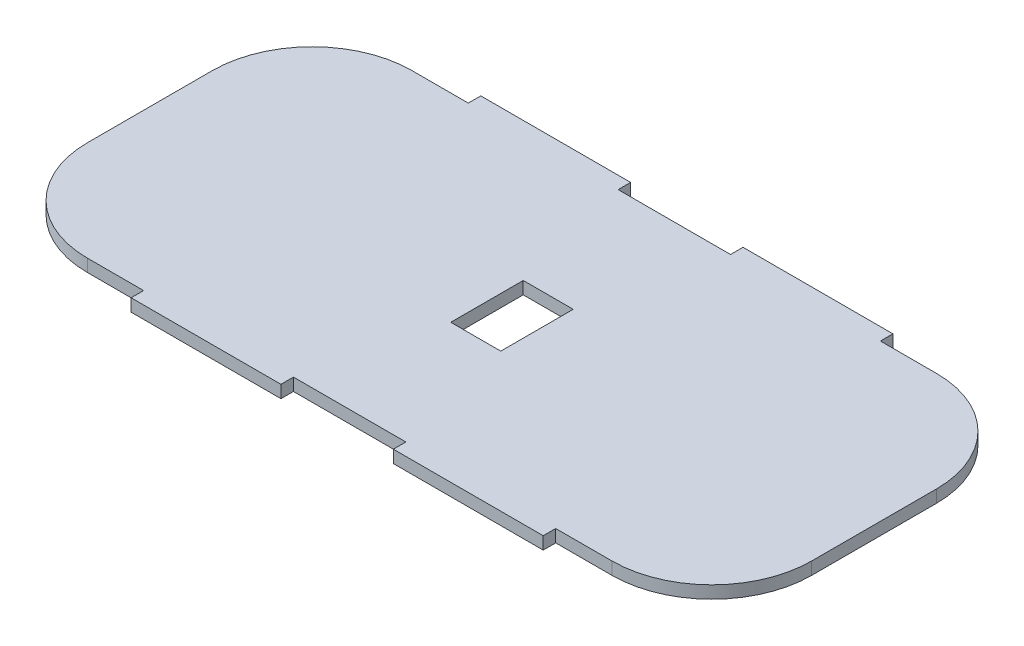
SolidWorks part; units mm, degrees
ref_plane "Front Plane" through (0, 0, 0) normal (0, 0, 1) x (1, 0, 0)
ref_plane "Top Plane" through (0, 0, 0) normal (0, 1, 0) x (1, 0, 0)
ref_plane "Right Plane" through (0, 0, 0) normal (1, 0, 0) x (0, 0, -1)
sketch "Sketch1" plane through (0, 0, 0) normal (0, 1, 0) x (1, 0, 0)
  line L0 (0, 83.3808) -> (0, -83.3808) construction
  line L1 (-52.5, 32.5) -> (-41.25, 32.5)
  line L2 (-72.5, 12.5) -> (-72.5, -12.5)
  line L3 (-52.5, -32.5) -> (-41.25, -32.5)
  line L4 (72.5, 12.5) -> (72.5, -12.5)
  line L5 (-72.5, 32.5) -> (72.5, -32.5) construction
  line L6 (-72.5, -32.5) -> (72.5, 32.5) construction
  line L7 (136.9216, 0) -> (-136.9216, 0) construction
  line L11 (-41.25, 35) -> (-11.25, 35)
  line L12 (-41.25, 35) -> (-41.25, 32.5)
  line L14 (-11.25, 35) -> (-11.25, 32.5)
  line L15 (41.25, 32.5) -> (52.5, 32.5)
  line L16 (-11.25, -32.5) -> (11.25, -32.5)
  line L17 (-11.25, -35) -> (-11.25, -32.5)
  line L18 (-41.25, -35) -> (-11.25, -35)
  line L19 (-41.25, -35) -> (-41.25, -32.5)
  line L20 (41.25, -35) -> (41.25, -32.5)
  line L21 (41.25, -35) -> (11.25, -35)
  line L22 (11.25, -35) -> (11.25, -32.5)
  line L25 (11.25, 35) -> (11.25, 32.5)
  line L26 (41.25, 35) -> (11.25, 35)
  line L27 (41.25, 35) -> (41.25, 32.5)
  line L28 (-11.25, 32.5) -> (11.25, 32.5)
  line L31 (41.25, -32.5) -> (52.5, -32.5)
  arc A0 (52.5, 32.5) -> (72.5, 12.5) centre (52.5, 12.5) cw
  arc A1 (72.5, -12.5) -> (52.5, -32.5) centre (52.5, -12.5) cw
  arc A2 (-52.5, -32.5) -> (-72.5, -12.5) centre (-52.5, -12.5) cw
  arc A3 (-72.5, 12.5) -> (-52.5, 32.5) centre (-52.5, 12.5) cw
  point P0 (0, 0)
  point P18 (-26.25, 32.5)
  point P21 (0, 0)
  point P24 (0, 0)
  dimension "D3" = 20
  dimension "D1" = 145
  dimension "D2" = 65
extrude "Boss-Extrude2" add sketch "Sketch1" along normal blind 2.5
sketch "Sketch3" plane through (0, 0, 0) normal (0, -1, 0) x (1, 0, 0)
  line L1 (-5, 7.25) -> (5, 7.25)
  line L2 (-5, 7.25) -> (-5, -7.25)
  line L3 (-5, -7.25) -> (5, -7.25)
  line L4 (5, 7.25) -> (5, -7.25)
  line L5 (-5, 7.25) -> (5, -7.25) construction
  line L6 (-5, -7.25) -> (5, 7.25) construction
  point P0 (0, 0)
  dimension "D1" = 10
  dimension "D2" = 14.5
extrude "Cut-Extrude3" cut sketch "Sketch3" against normal blind 40
